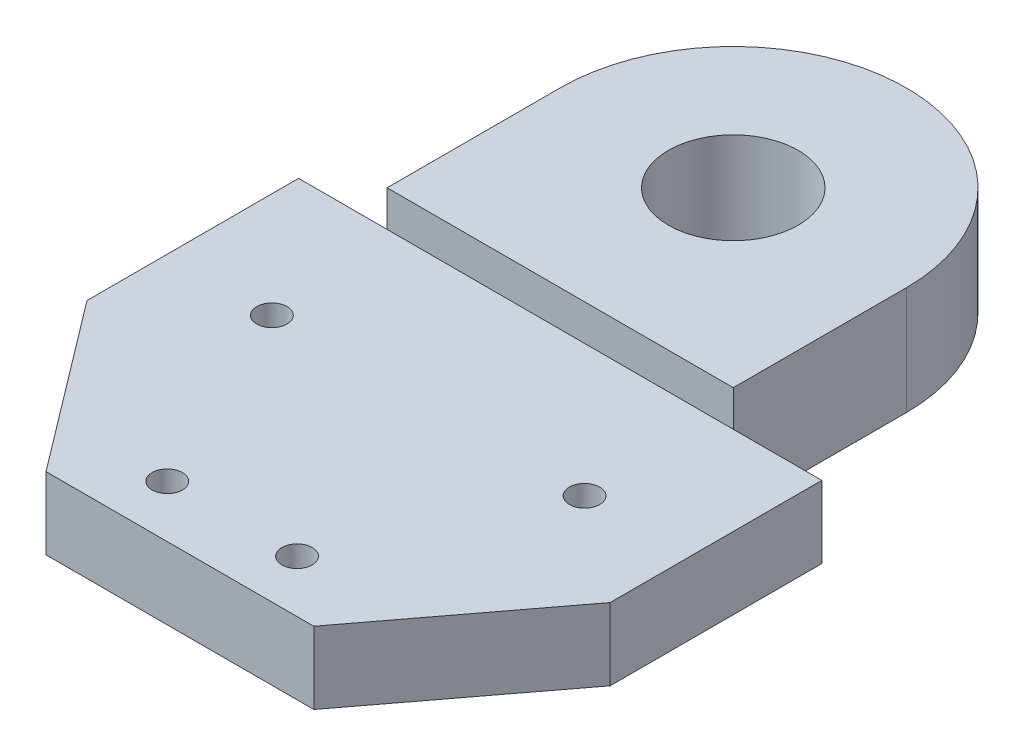
SolidWorks part; units mm, degrees
ref_plane "Front Plane" through (0, 0, 0) normal (0, 0, 1) x (1, 0, 0)
ref_plane "Top Plane" through (0, 0, 0) normal (0, 1, 0) x (1, 0, 0)
ref_plane "Right Plane" through (0, 0, 0) normal (1, 0, 0) x (0, 0, -1)
sketch "Sketch1" plane through (0, 0, 0) normal (0, 1, 0) x (1, 0, 0)
  line L0 (7.5, 0) -> (-7.5, 0) construction
  line L1 (-7.5, 0) -> (-18.0655, 22.6577) construction
  line L2 (7.5, 0) -> (18.0655, 22.6577) construction
  line L3 (-18.0655, 22.6577) -> (18.0655, 22.6577) construction
  line L4 (-30.225, 13.454) -> (-15.4735, -6.0352)
  line L5 (30.225, 13.454) -> (15.4735, -6.0352)
  line L6 (-15.4735, -6.0352) -> (15.4735, -6.0352)
  line L7 (-18.0655, 37.9077) -> (18.0655, 37.9077)
  line L8 (-30.225, 13.454) -> (-30.225, 37.9077)
  line L9 (-30.225, 37.9077) -> (-18.0655, 37.9077)
  line L10 (30.225, 13.454) -> (30.225, 37.9077)
  line L11 (30.225, 37.9077) -> (18.0655, 37.9077)
  circle A0 centre (-18.0655, 22.6577) radius 15.25 construction
  circle A1 centre (18.0655, 22.6577) radius 15.25 construction
  circle A2 centre (-7.5, 0) radius 10 construction
  circle A3 centre (7.5, 0) radius 10 construction
  arc A4 (-30.225, 13.454) -> (-18.0655, 37.9077) centre (-18.0655, 22.6577) cw construction
  arc A5 (30.225, 13.454) -> (18.0655, 37.9077) centre (18.0655, 22.6577) ccw construction
  circle A6 centre (-18.0655, 22.6577) radius 1.75
  circle A7 centre (18.0655, 22.6577) radius 1.75
  circle A8 centre (7.5, 0) radius 1.75
  circle A9 centre (-7.5, 0) radius 1.75
  point P4 (0, 0)
  dimension "D7" = 20
  dimension "D8" = 20
  dimension "D9" = 30.5
  dimension "D10" = 30.5
  dimension "D11" = 3.5
  dimension "D1" = 15
  dimension "D2" = 65
  dimension "D3" = 65
  dimension "D4" = 25
  dimension "D5" = 25
  dimension "D6" = 36.1309
extrude "Boss-Extrude1" add sketch "Sketch1" along normal blind 8.3333
sketch "Sketch2" plane through (0, 0, 0) normal (0, 1, 0) x (1, 0, 0)
  line L0 (0, 37.9077) -> (0, 77.9077) construction
  line L1 (30.225, 37.9077) -> (-30.225, 37.9077) construction
  line L5 (-20, 57.9077) -> (-20, 37.9077)
  line L6 (30.225, 37.9077) -> (-30.225, 37.9077) construction
  line L7 (-20, 37.9077) -> (20, 37.9077)
  line L8 (20, 37.9077) -> (20, 57.9077)
  arc A0 (20, 57.9077) -> (-20, 57.9077) centre (0, 57.9077) ccw
  circle A1 centre (0, 57.9077) radius 7.5
  dimension "D2" = 15
  dimension "D1" = 40
extrude "Boss-Extrude2" add sketch "Sketch2" along normal blind 12.5
